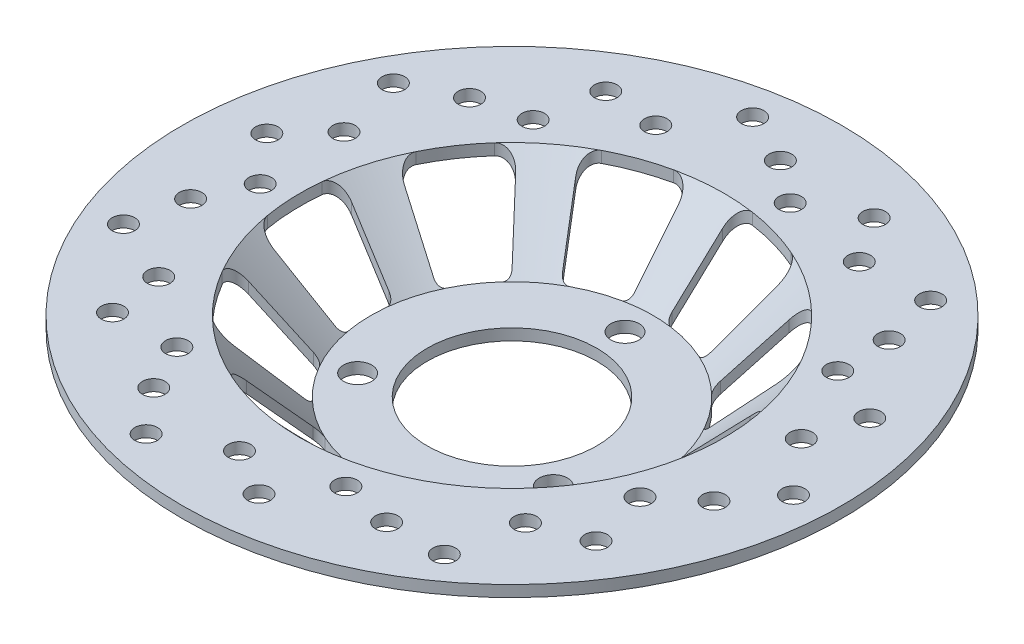
SolidWorks part; units mm, degrees
ref_plane "Front Plane" through (0, 0, 0) normal (0, 0, 1) x (1, 0, 0)
ref_plane "Top Plane" through (0, 0, 0) normal (0, 1, 0) x (1, 0, 0)
ref_plane "Right Plane" through (0, 0, 0) normal (1, 0, 0) x (0, 0, -1)
sketch "Sketch3" plane through (0, 0, 0) normal (0, 0, 1) x (1, 0, 0)
  line L0 (0, 0) -> (0, 47.3117) construction
  line L1 (-30, 0) -> (-50, 0)
  line L2 (-50, 0) -> (-75, 25)
  line L3 (-75, 25) -> (-116.655, 25)
  line L4 (-116.655, 25) -> (-116.655, 29)
  line L5 (-116.655, 29) -> (-75, 29)
  line L6 (-75, 29) -> (-50, 4)
  line L7 (-50, 4) -> (-30, 4)
  line L8 (-30, 4) -> (-30, 0)
  dimension "D1" = 4
  dimension "D2" = 25
  dimension "D3" = 50
  dimension "D4" = 116.655
  dimension "D5" = 50
  dimension "D6" = 75
  dimension "D7" = 75
  dimension "D8" = 30
  dimension "D9" = 30
revolve "Revolve3" add sketch "Sketch3" angle 360 about L0
sketch "Sketch4" plane through (0, 4, 0) normal (0, 1, 0) x (1, 0, 0)
  circle A0 centre (0, 40) radius 5
  circle A1 centre (34.641, -20) radius 5
  circle A2 centre (-34.641, -20) radius 5
  point P10 (0, 0)
  dimension "D1" = 40
  dimension "D2" = 3
extrude "Cut-Extrude1" cut sketch "Sketch4" against normal through all
sketch "Sketch5" plane through (0, 29, 0) normal (0, 1, 0) x (1, 0, 0)
  line L1 (0, 0) -> (0, 116.655) construction
  line L2 (0, 0) -> (18.3815, 104.2469) construction
  line L4 (0, 0) -> (-19.7667, 112.1026) construction
  line L5 (-35.2373, 0) -> (68.5015, 0) construction
  line L6 (0, 0) -> (42.8082, 117.6146) construction
  line L7 (0, 0) -> (64.0001, 110.8514) construction
  circle A2 centre (0, 0) radius 116.655 construction
  circle A3 centre (0, 95) radius 4
  circle A4 centre (-18.2322, 103.4) radius 4
  circle A5 centre (14.7603, 83.71) radius 4
  circle A6 centre (69.4738, 78.7234) radius 4
  circle A7 centre (74.274, 59.2315) radius 4
  circle A8 centre (74.65, 40.6522) radius 4
  circle A9 centre (104.8646, -5.2336) radius 4
  circle A10 centre (92.6182, -21.1395) radius 4
  circle A11 centre (78.3267, -33.0175) radius 4
  circle A12 centre (61.2902, -85.2495) radius 4
  circle A13 centre (41.219, -85.592) radius 4
  circle A14 centre (23.0218, -81.8244) radius 4
  circle A15 centre (-28.4369, -101.0708) radius 4
  circle A16 centre (-41.219, -85.592) radius 4
  circle A17 centre (-49.619, -69.0158) radius 4
  circle A18 centre (-96.7505, -40.7838) radius 4
  circle A19 centre (-92.6182, -21.1395) radius 4
  circle A20 centre (-84.8957, -4.237) radius 4
  circle A21 centre (-92.209, 50.2143) radius 4
  circle A22 centre (-74.274, 59.2315) radius 4
  circle A23 centre (-56.2442, 63.7324) radius 4
  circle A24 centre (34.2023, 93.97) radius 4
  circle A25 centre (44.9987, 77.94) radius 4
  circle A26 centre (94.7935, 31.8489) radius 4
  circle A27 centre (88.9922, 13.4134) radius 4
  circle A28 centre (84.0033, -54.2551) radius 4
  circle A29 centre (65.9727, -61.2138) radius 4
  circle A30 centre (9.9569, -99.5039) radius 4
  circle A31 centre (-6.7255, -89.7457) radius 4
  circle A32 centre (-71.5872, -69.8242) radius 4
  circle A33 centre (-74.3593, -50.6973) radius 4
  circle A34 centre (-99.2247, 12.4345) radius 4
  circle A35 centre (-85.999, 26.5272) radius 4
  circle A36 centre (-52.1439, 85.3298) radius 4
  circle A37 centre (-32.8797, 83.7762) radius 4
  point P56 (0, 0)
  point P86 (0, 0)
  dimension "D12" = 8
  dimension "D1" = 10
  dimension "D2" = 95
  dimension "D3" = 83.71
  dimension "D4" = 103.4
  dimension "D5" = 10
  dimension "D7" = 20
  dimension "D8" = 10
  dimension "D9" = 93.97
  dimension "D10" = 77.94
  dimension "D6" = 7
  dimension "D11" = 7
extrude "Cut-Extrude2" cut sketch "Sketch5" against normal up to surface (4 mm away) up to face at (0, 25, -75)
sketch "Sketch6" plane through (0, 29, 0) normal (0, 1, 0) x (1, 0, 0)
  line L0 (0, 0) -> (0, 116.655) construction
  line L1 (0, 0) -> (-39.8984, 109.6198) construction
  line L2 (5.1452, 69.4359) -> (4.5402, 52.1133)
  line L3 (-9.9762, 68.9078) -> (-8.1644, 51.6696)
  line L4 (-36.6509, 59.199) -> (-26.9583, 44.8292)
  line L5 (32.4321, 61.6115) -> (23.7655, 46.6005)
  line L6 (44.9759, 53.1505) -> (34.3045, 39.4918)
  line L7 (62.4524, 30.7816) -> (46.6178, 23.7316)
  line L8 (67.6274, 16.5635) -> (50.9657, 11.7859)
  line L9 (68.6181, -11.8057) -> (51.6637, -8.202)
  line L10 (64.4475, -26.3502) -> (48.1596, -20.4219)
  line L11 (48.5739, -49.8837) -> (36.9758, -37.0027)
  line L12 (36.6509, -59.199) -> (26.9583, -44.8292)
  line L13 (9.9762, -68.9078) -> (8.1644, -51.6696)
  line L14 (-5.1452, -69.4359) -> (-4.5402, -52.1133)
  line L15 (-32.4321, -61.6115) -> (-23.7655, -46.6005)
  line L16 (-44.9759, -53.1505) -> (-34.3045, -39.4918)
  line L17 (-62.4524, -30.7816) -> (-46.6178, -23.7316)
  line L18 (-67.6274, -16.5635) -> (-50.9657, -11.7859)
  line L19 (-68.6181, 11.8057) -> (-51.6637, 8.202)
  line L20 (-64.4475, 26.3502) -> (-48.1596, 20.4219)
  line L21 (-48.5739, 49.8837) -> (-36.9758, 37.0027)
  circle A0 centre (0, 0) radius 116.655 construction
  arc A2 (-10.1435, 48.9603) -> (-23.7006, 44.0259) centre (0, 0) ccw
  arc A3 (-16.0166, 73.2698) -> (-34.8275, 66.4232) centre (0, 0) ccw
  arc A4 (-9.9762, 68.9078) -> (-16.0166, 73.2698) centre (-14.9488, 68.3852) ccw
  arc A5 (-10.1435, 48.9603) -> (-8.1644, 51.6696) centre (-10.6507, 51.4083) ccw
  arc A6 (-23.7006, 44.0259) -> (-26.9583, 44.8292) centre (-24.8857, 46.2272) cw
  arc A7 (-36.6509, 59.199) -> (-34.8275, 66.4232) centre (-32.5057, 61.995) cw
  arc A8 (30.1092, 68.6909) -> (10.8666, 74.2086) centre (0, 0) ccw
  arc A9 (5.1452, 69.4359) -> (10.8666, 74.2086) centre (10.1421, 69.2614) cw
  arc A10 (6.7035, 49.5486) -> (4.5402, 52.1133) centre (7.0387, 52.026) cw
  arc A11 (20.5718, 45.5719) -> (6.7035, 49.5486) centre (0, 0) ccw
  arc A12 (20.5718, 45.5719) -> (23.7655, 46.6005) centre (21.6004, 47.8505) ccw
  arc A13 (32.4321, 61.6115) -> (30.1092, 68.6909) centre (28.1019, 64.1115) ccw
  arc A14 (64.7343, 37.8743) -> (52.41, 53.6488) centre (0, 0) ccw
  arc A15 (44.9759, 53.1505) -> (52.41, 53.6488) centre (48.916, 50.0722) cw
  arc A16 (34.5472, 36.1454) -> (34.3045, 39.4918) centre (36.2746, 37.9527) cw
  arc A17 (43.4295, 24.7766) -> (34.5472, 36.1454) centre (0, 0) ccw
  arc A18 (43.4295, 24.7766) -> (46.6178, 23.7316) centre (45.6009, 26.0155) ccw
  arc A19 (62.4524, 30.7816) -> (64.7343, 37.8743) centre (60.4187, 35.3494) ccw
  arc A20 (74.6332, -7.4089) -> (73.9345, 12.597) centre (0, 0) ccw
  arc A21 (67.6274, 16.5635) -> (73.9345, 12.597) centre (69.0056, 11.7572) cw
  arc A22 (49.195, 8.9359) -> (50.9657, 11.7859) centre (51.6548, 9.3827) cw
  arc A23 (49.6985, -5.4825) -> (49.195, 8.9359) centre (0, 0) ccw
  arc A24 (49.6985, -5.4825) -> (51.6637, -8.202) centre (52.1834, -5.7566) ccw
  arc A25 (68.6181, -11.8057) -> (74.6332, -7.4089) centre (69.6576, -6.915) ccw
  arc A26 (56.0246, -49.8622) -> (67.2186, -33.2664) centre (0, 0) ccw
  arc A27 (64.4475, -26.3502) -> (67.2186, -33.2664) centre (62.7374, -31.0487) cw
  arc A28 (45.052, -21.6868) -> (48.1596, -20.4219) centre (47.3046, -22.7711) cw
  arc A29 (36.9844, -33.6475) -> (45.052, -21.6868) centre (0, 0) ccw
  arc A30 (36.9844, -33.6475) -> (36.9758, -37.0027) centre (38.8337, -35.3298) ccw
  arc A31 (48.5739, -49.8837) -> (56.0246, -49.8622) centre (52.2897, -46.5381) ccw
  arc A32 (16.0166, -73.2698) -> (34.8275, -66.4232) centre (0, 0) ccw
  arc A33 (36.6509, -59.199) -> (34.8275, -66.4232) centre (32.5057, -61.995) cw
  arc A34 (23.7006, -44.0259) -> (26.9583, -44.8292) centre (24.8857, -46.2272) cw
  arc A35 (10.1435, -48.9603) -> (23.7006, -44.0259) centre (0, 0) ccw
  arc A36 (10.1435, -48.9603) -> (8.1644, -51.6696) centre (10.6507, -51.4083) ccw
  arc A37 (9.9762, -68.9078) -> (16.0166, -73.2698) centre (14.9488, -68.3852) ccw
  arc A38 (-30.1092, -68.6909) -> (-10.8666, -74.2086) centre (0, 0) ccw
  arc A39 (-5.1452, -69.4359) -> (-10.8666, -74.2086) centre (-10.1421, -69.2614) cw
  arc A40 (-6.7035, -49.5486) -> (-4.5402, -52.1133) centre (-7.0387, -52.026) cw
  arc A41 (-20.5718, -45.5719) -> (-6.7035, -49.5486) centre (0, 0) ccw
  arc A42 (-20.5718, -45.5719) -> (-23.7655, -46.6005) centre (-21.6004, -47.8505) ccw
  arc A43 (-32.4321, -61.6115) -> (-30.1092, -68.6909) centre (-28.1019, -64.1115) ccw
  arc A44 (-64.7343, -37.8743) -> (-52.41, -53.6488) centre (0, 0) ccw
  arc A45 (-44.9759, -53.1505) -> (-52.41, -53.6488) centre (-48.916, -50.0722) cw
  arc A46 (-34.5472, -36.1454) -> (-34.3045, -39.4918) centre (-36.2746, -37.9527) cw
  arc A47 (-43.4295, -24.7766) -> (-34.5472, -36.1454) centre (0, 0) ccw
  arc A48 (-43.4295, -24.7766) -> (-46.6178, -23.7316) centre (-45.6009, -26.0155) ccw
  arc A49 (-62.4524, -30.7816) -> (-64.7343, -37.8743) centre (-60.4187, -35.3494) ccw
  arc A50 (-74.6332, 7.4089) -> (-73.9345, -12.597) centre (0, 0) ccw
  arc A51 (-67.6274, -16.5635) -> (-73.9345, -12.597) centre (-69.0056, -11.7572) cw
  arc A52 (-49.195, -8.9359) -> (-50.9657, -11.7859) centre (-51.6548, -9.3827) cw
  arc A53 (-49.6985, 5.4825) -> (-49.195, -8.9359) centre (0, 0) ccw
  arc A54 (-49.6985, 5.4825) -> (-51.6637, 8.202) centre (-52.1834, 5.7566) ccw
  arc A55 (-68.6181, 11.8057) -> (-74.6332, 7.4089) centre (-69.6576, 6.915) ccw
  arc A56 (-56.0246, 49.8622) -> (-67.2186, 33.2664) centre (0, 0) ccw
  arc A57 (-64.4475, 26.3502) -> (-67.2186, 33.2664) centre (-62.7374, 31.0487) cw
  arc A58 (-45.052, 21.6868) -> (-48.1596, 20.4219) centre (-47.3046, 22.7711) cw
  arc A59 (-36.9844, 33.6475) -> (-45.052, 21.6868) centre (0, 0) ccw
  arc A60 (-36.9844, 33.6475) -> (-36.9758, 37.0027) centre (-38.8337, 35.3298) ccw
  arc A61 (-48.5739, 49.8837) -> (-56.0246, 49.8622) centre (-52.2897, 46.5381) ccw
  point P130 (0, 0)
  dimension "D3" = 100
  dimension "D4" = 5
  dimension "D5" = 2.5
  dimension "D7" = 75
  dimension "D1" = 20
  dimension "D2" = 10
  dimension "D6" = 20
extrude "Cut-Extrude3" cut sketch "Sketch6" against normal up to surface (29 mm away) up to face at (0, 0, -35)
